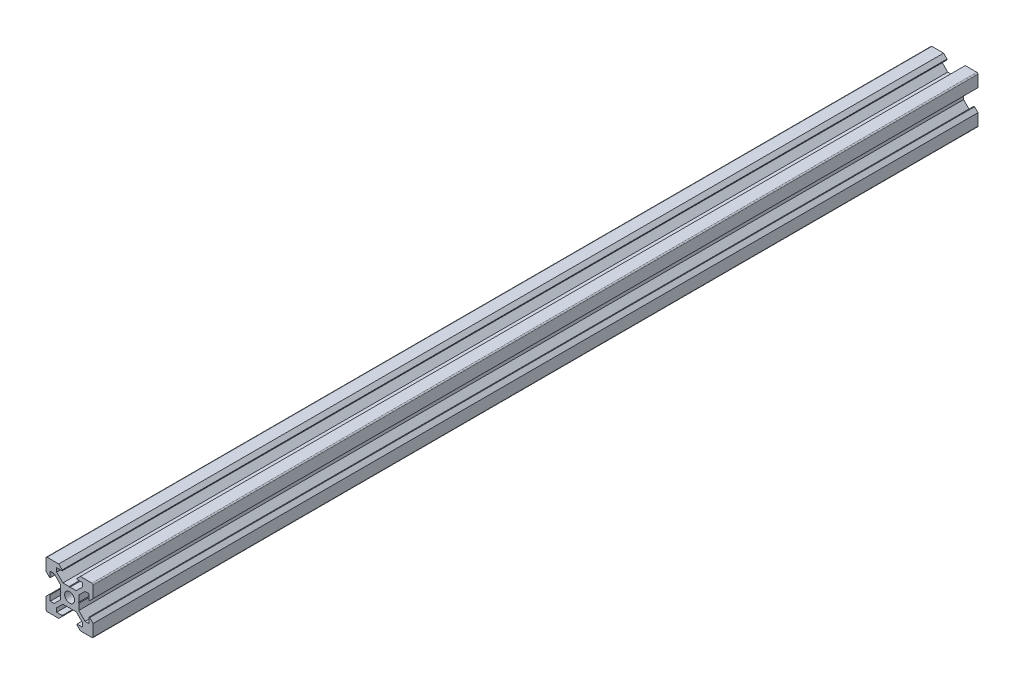
SolidWorks part; units mm, degrees
material "6061-T6 (SS)"
ref_plane "Front Plane" through (0, 0, 0) normal (0, 0, 1) x (1, 0, 0)
ref_plane "Top Plane" through (0, 0, 0) normal (0, 1, 0) x (1, 0, 0)
ref_plane "Right Plane" through (0, 0, 0) normal (1, 0, 0) x (0, 0, -1)
sketch "Sketch1" plane through (0, 0, 0) normal (0, 0, 1) x (1, 0, 0)
  line L1 (9.5, -10) -> (-9.5, -10)
  line L2 (10, -9.5) -> (10, 9.5)
  line L3 (9.5, 10) -> (-9.5, 10)
  line L4 (-10, -9.5) -> (-10, 9.5)
  line L5 (10, -10) -> (-10, 10) construction
  line L6 (10, 10) -> (-10, -10) construction
  circle A0 centre (0, 0) radius 2.1
  arc A1 (-9.5, 10) -> (-10, 9.5) centre (-9.5, 9.5) ccw
  arc A2 (10, 9.5) -> (9.5, 10) centre (9.5, 9.5) ccw
  arc A3 (9.5, -10) -> (10, -9.5) centre (9.5, -9.5) ccw
  arc A4 (-9.5, -10) -> (-10, -9.5) centre (-9.5, -9.5) cw
  point P0 (0, 0)
  line B0 (0, 0) -> (0, 10) construction
  line B1 (0, 3.69) -> (-0.21, 3.9)
  line B2 (-0.21, 3.9) -> (-2.8393, 3.9)
  line B3 (-2.8393, 3.9) -> (-5.5, 6.5607)
  line B4 (-5.5, 6.5607) -> (-5.5, 8.2)
  line B5 (-5.5, 8.2) -> (-3.125, 8.2)
  line B6 (-3.125, 8.2) -> (-3.125, 8.545)
  line B7 (-3.125, 8.545) -> (-4.58, 10)
  line B8 (-4.58, 10) -> (4.58, 10)
  line B9 (0, 0) -> (-5.9132, 5.9132) construction
  line B10 (3.125, 8.545) -> (4.58, 10)
  line B11 (3.125, 8.2) -> (3.125, 8.545)
  line B12 (5.5, 8.2) -> (3.125, 8.2)
  line B13 (5.5, 6.5607) -> (5.5, 8.2)
  line B14 (2.8393, 3.9) -> (5.5, 6.5607)
  line B15 (0.21, 3.9) -> (2.8393, 3.9)
  line B16 (0, 3.69) -> (0.21, 3.9)
  line B17 (0, 0) -> (-10, 0) construction
  line B18 (-3.69, 0) -> (-3.9, -0.21)
  line B19 (-3.9, -0.21) -> (-3.9, -2.8393)
  line B20 (-3.9, -2.8393) -> (-6.5607, -5.5)
  line B21 (-6.5607, -5.5) -> (-8.2, -5.5)
  line B22 (-8.2, -5.5) -> (-8.2, -3.125)
  line B23 (-8.2, -3.125) -> (-8.545, -3.125)
  line B24 (-8.545, -3.125) -> (-10, -4.58)
  line B25 (-10, -4.58) -> (-10, 4.58)
  line B26 (0, 0) -> (-5.9132, -5.9132) construction
  line B27 (-8.545, 3.125) -> (-10, 4.58)
  line B28 (-8.2, 3.125) -> (-8.545, 3.125)
  line B29 (-8.2, 5.5) -> (-8.2, 3.125)
  line B30 (-6.5607, 5.5) -> (-8.2, 5.5)
  line B31 (-3.9, 2.8393) -> (-6.5607, 5.5)
  line B32 (-3.9, 0.21) -> (-3.9, 2.8393)
  line B33 (-3.69, 0) -> (-3.9, 0.21)
  line B34 (0, 0) -> (0, -10) construction
  line B35 (0, -3.69) -> (0.21, -3.9)
  line B36 (0.21, -3.9) -> (2.8393, -3.9)
  line B37 (2.8393, -3.9) -> (5.5, -6.5607)
  line B38 (5.5, -6.5607) -> (5.5, -8.2)
  line B39 (5.5, -8.2) -> (3.125, -8.2)
  line B40 (3.125, -8.2) -> (3.125, -8.545)
  line B41 (3.125, -8.545) -> (4.58, -10)
  line B42 (4.58, -10) -> (-4.58, -10)
  line B43 (0, 0) -> (5.9132, -5.9132) construction
  line B44 (-3.125, -8.545) -> (-4.58, -10)
  line B45 (-3.125, -8.2) -> (-3.125, -8.545)
  line B46 (-5.5, -8.2) -> (-3.125, -8.2)
  line B47 (-5.5, -6.5607) -> (-5.5, -8.2)
  line B48 (-2.8393, -3.9) -> (-5.5, -6.5607)
  line B49 (-0.21, -3.9) -> (-2.8393, -3.9)
  line B50 (0, -3.69) -> (-0.21, -3.9)
  line B51 (0, 0) -> (10, 0) construction
  line B52 (3.69, 0) -> (3.9, 0.21)
  line B53 (3.9, 0.21) -> (3.9, 2.8393)
  line B54 (3.9, 2.8393) -> (6.5607, 5.5)
  line B55 (6.5607, 5.5) -> (8.2, 5.5)
  line B56 (8.2, 5.5) -> (8.2, 3.125)
  line B57 (8.2, 3.125) -> (8.545, 3.125)
  line B58 (8.545, 3.125) -> (10, 4.58)
  line B59 (10, 4.58) -> (10, -4.58)
  line B60 (0, 0) -> (5.9132, 5.9132) construction
  line B61 (8.545, -3.125) -> (10, -4.58)
  line B62 (8.2, -3.125) -> (8.545, -3.125)
  line B63 (8.2, -5.5) -> (8.2, -3.125)
  line B64 (6.5607, -5.5) -> (8.2, -5.5)
  line B65 (3.9, -2.8393) -> (6.5607, -5.5)
  line B66 (3.9, -0.21) -> (3.9, -2.8393)
  line B67 (3.69, 0) -> (3.9, -0.21)
  dimension "D1" = 4.2
  dimension "D3" = 0.5
  dimension "D2" = 20
sketch_block_instance "V Slot 1-4"
sketch_block "V Slot 1" parameters "D1"=10, "D2"=11, "D3"=4.3, "D4"=1.8, "D5"=0.21, "D6"=45, "D7"=9.16, "D8"=1.5, "D9"=6.25
sketch_block_instance "V Slot 1-5"
sketch_block_instance "V Slot 1-6"
sketch_block_instance "V Slot 1-7"
extrude "Boss-Extrude1" add sketch "Sketch1" along normal mid plane 375.14 contours B67 B52 B53 B54 B55 B56 B57 B58 L2 A2 L3 B10 B11 B12 B13 B14 B15 B16 B1 B2 B3 B4 B5 B6 B7 A1 L4 B27 B28 B29 B30 B31 B32 B33 B18 B19 B20 B21 B22 B23 B24 A4 L1 B44 B45 B46 B47 B48 B49
